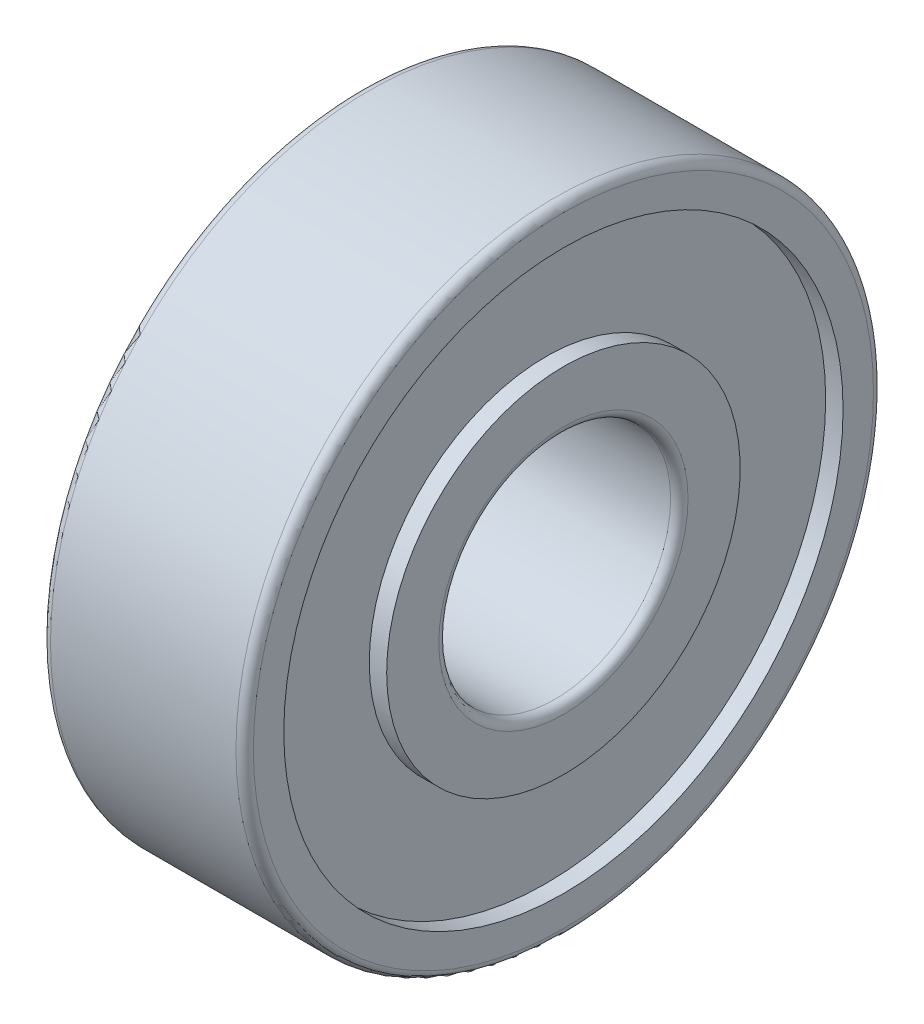
SolidWorks part; units mm, degrees
ref_plane "Front Plane" through (0, 0, 0) normal (0, 0, 1) x (1, 0, 0)
ref_plane "Top Plane" through (0, 0, 0) normal (0, 1, 0) x (1, 0, 0)
ref_plane "Right Plane" through (0, 0, 0) normal (1, 0, 0) x (0, 0, -1)
sketch "Sketch1" plane through (0, 0, 0) normal (0, 0, 1) x (1, 0, 0)
  line L0 (-7, 0) -> (0, 0) construction
  line L1 (-7, 4) -> (0, 4)
  line L2 (-7, 11) -> (0, 11)
  line L3 (-7, 11) -> (-7, 9.65)
  line L4 (-7, 9.65) -> (-6.4, 9.65)
  line L5 (0, 11) -> (0, 9.65)
  line L6 (-6.4, 9.65) -> (-6.4, 6.1)
  line L7 (-6.4, 6.1) -> (-7, 6.1)
  line L8 (-7, 6.1) -> (-7, 4)
  line L9 (0, 9.65) -> (-0.6, 9.65)
  line L10 (-0.6, 9.65) -> (-0.6, 6.1)
  line L11 (-0.6, 6.1) -> (0, 6.1)
  line L12 (0, 6.1) -> (0, 4)
  dimension "MSM_14" = 7
  dimension "D_s" = 8
  dimension "MSM_13" = 22
  dimension "MSM_10" = 19.3
  dimension "MSM_11" = 12.2
  dimension "MSM_12" = 0.6
revolve "Revolve1" add sketch "Sketch1" angle 360 about L0
fillet "Fillet1" radius 0.3 2 edges at (0, 0, 11) (-7, 0, 11)
fillet "Fillet2" radius 0.3 2 edges at (0, 0, 4) (-7, 0, 4)
